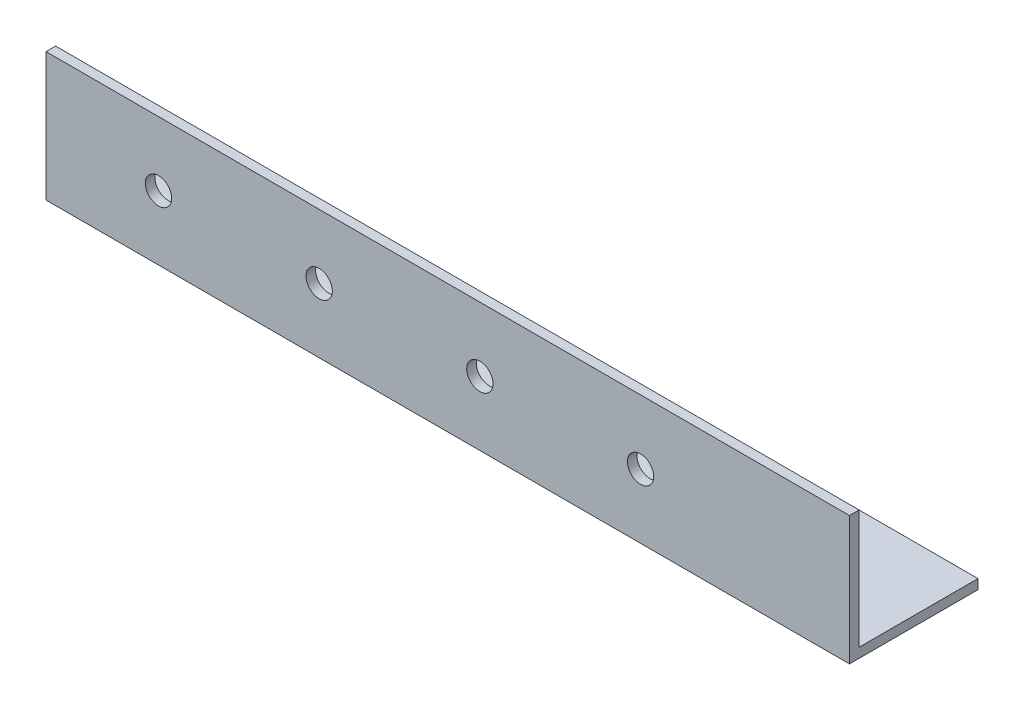
SolidWorks part; units mm, degrees
ref_plane "Спереди" through (0, 0, 0) normal (0, 0, 1) x (1, 0, 0)
ref_plane "Сверху" through (0, 0, 0) normal (0, 1, 0) x (1, 0, 0)
ref_plane "Справа" through (0, 0, 0) normal (1, 0, 0) x (0, 0, -1)
sketch "Эскиз1" plane through (0, 0, 0) normal (1, 0, 0) x (0, 0, -1)
  line L0 (0, 0) -> (0, 40)
  line L1 (0, 0) -> (40, 0)
extrude "Вытянуть-Тонкостенный1" add sketch "Эскиз1" along normal blind 250 thin
sketch "Эскиз2" plane through (0, 0, 0) normal (0, 0, 1) x (1, 0, 0)
  line L0 (0, 40) -> (0, 0) construction
  circle A0 centre (35, 20) radius 4.1
  circle A1 centre (85, 20) radius 4.1
  circle A2 centre (135, 20) radius 4.1
  circle A3 centre (185, 20) radius 4.1
  dimension "D1" = 4
  dimension "D2" = 35
extrude "Вырез-Вытянуть1" cut sketch "Эскиз2" against normal blind 10
